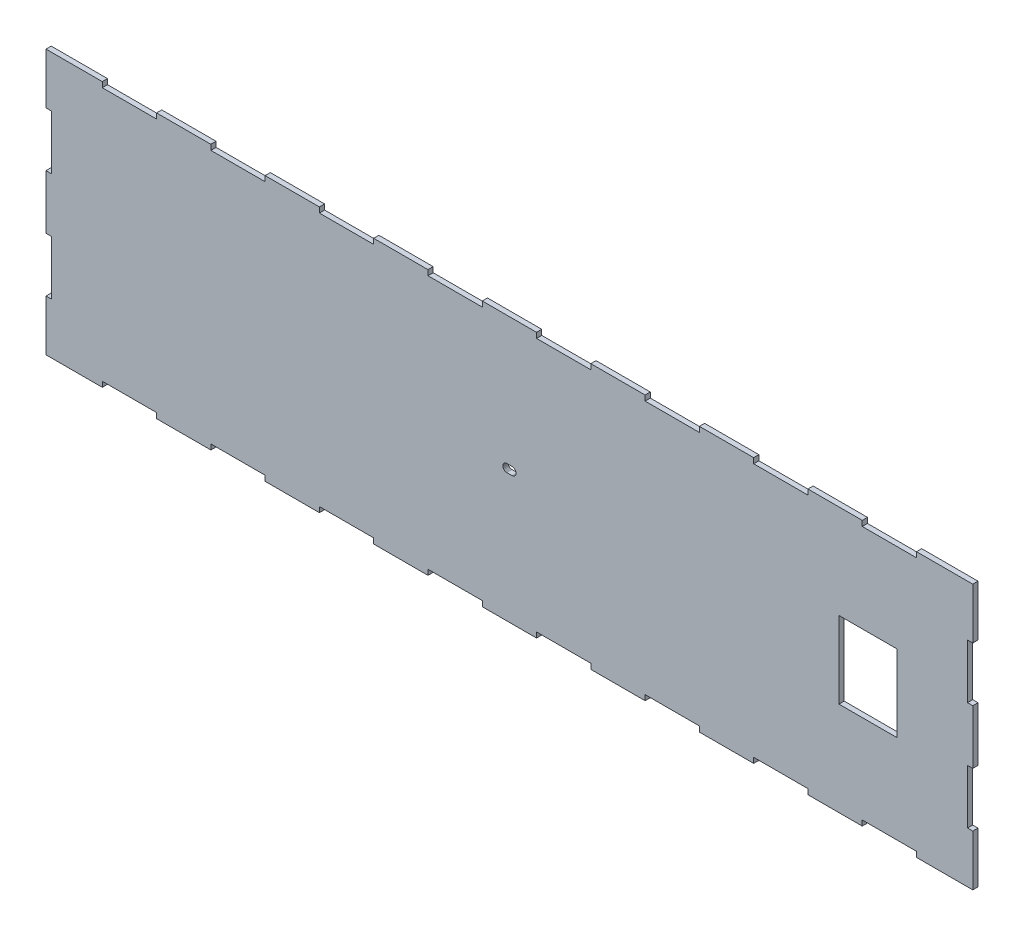
SolidWorks part; units mm, degrees
ref_plane "Front Plane" through (0, 0, 0) normal (0, 0, 1) x (1, 0, 0)
ref_plane "Top Plane" through (0, 0, 0) normal (0, 1, 0) x (1, 0, 0)
ref_plane "Right Plane" through (0, 0, 0) normal (1, 0, 0) x (0, 0, -1)
sketch "Sketch1" plane through (0, 0, 0) normal (0, 0, 1) x (1, 0, 0)
  line B0 (4705.35, 2489.2) -> (5226.05, 2489.2)
  line B1 (4184.65, 2540) -> (4705.35, 2540)
  line B2 (50.8, 488.95) -> (50.8, 1009.65)
  line B3 (50.8, 1530.35) -> (50.8, 2051.05)
  line B4 (1060.45, 2540) -> (1581.15, 2540)
  line B5 (0, 0) -> (0, 488.95)
  line B6 (0, 488.95) -> (50.8, 488.95)
  line B7 (50.8, 1009.65) -> (0, 1009.65)
  line B8 (0, 1009.65) -> (0, 1530.35)
  line B9 (0, 1530.35) -> (50.8, 1530.35)
  line B10 (50.8, 2051.05) -> (0, 2051.05)
  line B11 (0, 2051.05) -> (0, 2540)
  line B12 (0, 2540) -> (539.75, 2540)
  line B13 (539.75, 2540) -> (539.75, 2489.2)
  line B14 (539.75, 2489.2) -> (1060.45, 2489.2)
  line B15 (1060.45, 2489.2) -> (1060.45, 2540)
  line B16 (1581.15, 2540) -> (1581.15, 2489.2)
  line B17 (1581.15, 2489.2) -> (2101.85, 2489.2)
  line B18 (2101.85, 2489.2) -> (2101.85, 2540)
  line B19 (2101.85, 2540) -> (2622.55, 2540)
  line B20 (2622.55, 2540) -> (2622.55, 2489.2)
  line B21 (2622.55, 2489.2) -> (3143.25, 2489.2)
  line B22 (3143.25, 2489.2) -> (3143.25, 2540)
  line B23 (3143.25, 2540) -> (3663.95, 2540)
  line B24 (3663.95, 2540) -> (3663.95, 2489.2)
  line B25 (3663.95, 2489.2) -> (4184.65, 2489.2)
  line B26 (4184.65, 2489.2) -> (4184.65, 2540)
  line B27 (4705.35, 2540) -> (4705.35, 2489.2)
  line B28 (5226.05, 2489.2) -> (5226.05, 2540)
  line B29 (5226.05, 2540) -> (5746.75, 2540)
  line B30 (5746.75, 2540) -> (5746.75, 2489.2)
  line B31 (5746.75, 2489.2) -> (6267.45, 2489.2)
  line B32 (6267.45, 2489.2) -> (6267.45, 2540)
  line B33 (6267.45, 2540) -> (6788.15, 2540)
  line B34 (6788.15, 2540) -> (6788.15, 2489.2)
  line B35 (6788.15, 2489.2) -> (7308.85, 2489.2)
  line B36 (7308.85, 2489.2) -> (7308.85, 2540)
  line B37 (7308.85, 2540) -> (7829.55, 2540)
  line B38 (7829.55, 2540) -> (7829.55, 2489.2)
  line B39 (7829.55, 2489.2) -> (8350.25, 2489.2)
  line B40 (8350.25, 2489.2) -> (8350.25, 2540)
  line B41 (8350.25, 2540) -> (8890, 2540)
  line B42 (8890, 2540) -> (8890, 2051.05)
  line B43 (8890, 2051.05) -> (8839.2, 2051.05)
  line B44 (8839.2, 2051.05) -> (8839.2, 1530.35)
  line B45 (8839.2, 1530.35) -> (8890, 1530.35)
  line B46 (8890, 1530.35) -> (8890, 1009.65)
  line B47 (8890, 1009.65) -> (8839.2, 1009.65)
  line B48 (8839.2, 1009.65) -> (8839.2, 488.95)
  line B49 (8839.2, 488.95) -> (8890, 488.95)
  line B50 (8890, 488.95) -> (8890, 0)
  line B51 (8890, 0) -> (8350.25, 0)
  line B52 (8350.25, 0) -> (8350.25, 50.8)
  line B53 (8350.25, 50.8) -> (7829.55, 50.8)
  line B54 (7829.55, 50.8) -> (7829.55, 0)
  line B55 (7829.55, 0) -> (7308.85, 0)
  line B56 (7308.85, 0) -> (7308.85, 50.8)
  line B57 (7308.85, 50.8) -> (6788.15, 50.8)
  line B58 (6788.15, 50.8) -> (6788.15, 0)
  line B59 (6788.15, 0) -> (6267.45, 0)
  line B60 (6267.45, 0) -> (6267.45, 50.8)
  line B61 (6267.45, 50.8) -> (5746.75, 50.8)
  line B62 (5746.75, 50.8) -> (5746.75, 0)
  line B63 (5746.75, 0) -> (5226.05, 0)
  line B64 (5226.05, 0) -> (5226.05, 50.8)
  line B65 (5226.05, 50.8) -> (4705.35, 50.8)
  line B66 (4705.35, 50.8) -> (4705.35, 0)
  line B67 (4705.35, 0) -> (4184.65, 0)
  line B68 (4184.65, 0) -> (4184.65, 50.8)
  line B69 (4184.65, 50.8) -> (3663.95, 50.8)
  line B70 (3663.95, 50.8) -> (3663.95, 0)
  line B71 (3663.95, 0) -> (3143.25, 0)
  line B72 (3143.25, 0) -> (3143.25, 50.8)
  line B73 (3143.25, 50.8) -> (2622.55, 50.8)
  line B74 (2622.55, 50.8) -> (2622.55, 0)
  line B75 (2622.55, 0) -> (2101.85, 0)
  line B76 (2101.85, 0) -> (2101.85, 50.8)
  line B77 (2101.85, 50.8) -> (1581.15, 50.8)
  line B78 (1581.15, 50.8) -> (1581.15, 0)
  line B79 (1581.15, 0) -> (1060.45, 0)
  line B80 (1060.45, 0) -> (1060.45, 50.8)
  line B81 (1060.45, 50.8) -> (539.75, 50.8)
  line B82 (539.75, 50.8) -> (539.75, 0)
  line B83 (539.75, 0) -> (0, 0)
  line B84 (4470.4, 1231.9) -> (4419.6, 1231.9)
  line B85 (4419.6, 1231.9) -> (4415.7045, 1232.0967)
  line B86 (4415.7045, 1232.0967) -> (4411.9215, 1232.6741)
  line B87 (4411.9215, 1232.6741) -> (4404.7698, 1234.8941)
  line B88 (4404.7698, 1234.8941) -> (4398.2979, 1238.4069)
  line B89 (4398.2979, 1238.4069) -> (4392.6592, 1243.0592)
  line B90 (4392.6592, 1243.0592) -> (4388.0069, 1248.6979)
  line B91 (4388.0069, 1248.6979) -> (4384.4941, 1255.1698)
  line B92 (4384.4941, 1255.1698) -> (4382.2741, 1262.3215)
  line B93 (4382.2741, 1262.3215) -> (4381.6967, 1266.1045)
  line B94 (4381.6967, 1266.1045) -> (4381.5, 1270)
  line B95 (4381.5, 1270) -> (4381.6967, 1273.8955)
  line B96 (4381.6967, 1273.8955) -> (4382.2741, 1277.6785)
  line B97 (4382.2741, 1277.6785) -> (4384.4941, 1284.8302)
  line B98 (4384.4941, 1284.8302) -> (4388.0069, 1291.3021)
  line B99 (4388.0069, 1291.3021) -> (4392.6592, 1296.9408)
  line B100 (4392.6592, 1296.9408) -> (4398.2979, 1301.5931)
  line B101 (4398.2979, 1301.5931) -> (4404.7698, 1305.1059)
  line B102 (4404.7698, 1305.1059) -> (4411.9215, 1307.3259)
  line B103 (4411.9215, 1307.3259) -> (4415.7045, 1307.9033)
  line B104 (4415.7045, 1307.9033) -> (4419.6, 1308.1)
  line B105 (4419.6, 1308.1) -> (4470.4, 1308.1)
  line B106 (4470.4, 1308.1) -> (4474.2955, 1307.9033)
  line B107 (4474.2955, 1307.9033) -> (4478.0785, 1307.3259)
  line B108 (4478.0785, 1307.3259) -> (4485.2302, 1305.1059)
  line B109 (4485.2302, 1305.1059) -> (4491.7021, 1301.5931)
  line B110 (4491.7021, 1301.5931) -> (4497.3408, 1296.9408)
  line B111 (4497.3408, 1296.9408) -> (4501.9931, 1291.3021)
  line B112 (4501.9931, 1291.3021) -> (4505.5059, 1284.8302)
  line B113 (4505.5059, 1284.8302) -> (4507.7259, 1277.6785)
  line B114 (4507.7259, 1277.6785) -> (4508.3033, 1273.8955)
  line B115 (4508.3033, 1273.8955) -> (4508.5, 1270)
  line B116 (4508.5, 1270) -> (4508.3033, 1266.1045)
  line B117 (4508.3033, 1266.1045) -> (4507.7259, 1262.3215)
  line B118 (4507.7259, 1262.3215) -> (4505.5059, 1255.1698)
  line B119 (4505.5059, 1255.1698) -> (4501.9931, 1248.6979)
  line B120 (4501.9931, 1248.6979) -> (4497.3408, 1243.0592)
  line B121 (4497.3408, 1243.0592) -> (4491.7021, 1238.4069)
  line B122 (4491.7021, 1238.4069) -> (4485.2302, 1234.8941)
  line B123 (4485.2302, 1234.8941) -> (4478.0785, 1232.6741)
  line B124 (4478.0785, 1232.6741) -> (4474.2955, 1232.0967)
  line B125 (4474.2955, 1232.0967) -> (4470.4, 1231.9)
  line B126 (7606.2055, 901.7) -> (7606.2055, 1638.3)
  line B127 (7606.2055, 1638.3) -> (8165.0055, 1638.3)
  line B128 (8165.0055, 1638.3) -> (8165.0055, 901.7)
  line B129 (8165.0055, 901.7) -> (7606.2055, 901.7)
sketch_block_instance "s3-1"
sketch_block "s3"
extrude "Boss-Extrude1" add sketch "Sketch1" along normal blind 50
scale "Scale1" scale about centroid uniform scaling yes scale factor 0.04
